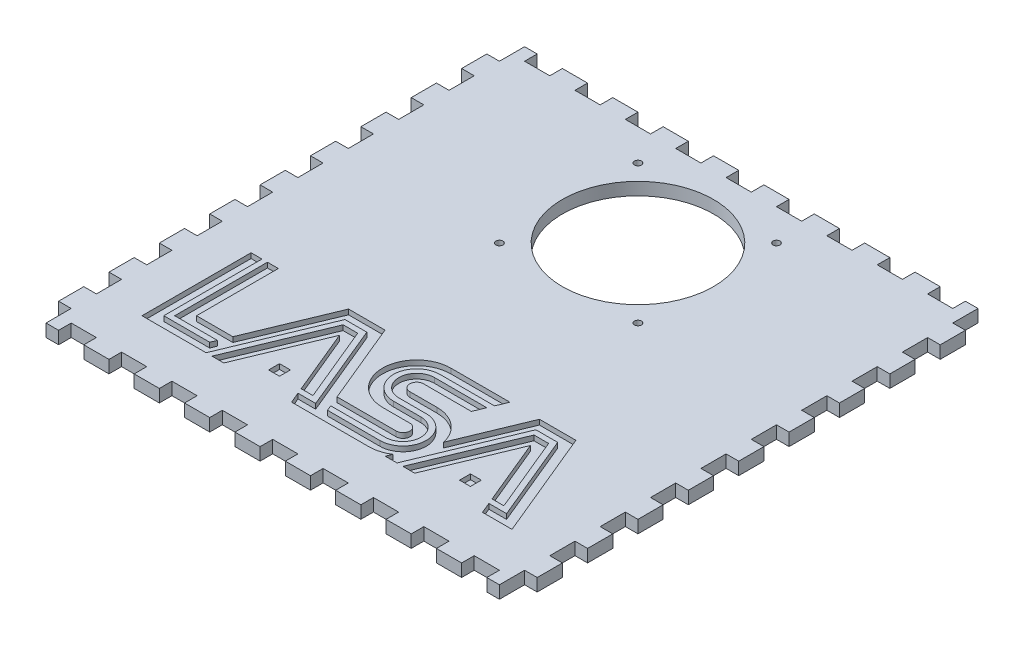
SolidWorks part; units mm, degrees
material "Pine"
ref_plane "Front Plane" through (0, 0, 0) normal (0, 0, 1) x (1, 0, 0)
ref_plane "Top Plane" through (0, 0, 0) normal (0, 1, 0) x (1, 0, 0)
ref_plane "Right Plane" through (0, 0, 0) normal (1, 0, 0) x (0, 0, -1)
sketch "Sketch1" plane through (0, 0, 0) normal (0, 1, 0) x (1, 0, 0)
  line L1 (0, 0) -> (241.3, 0)
  line L2 (0, 0) -> (0, 241.3)
  line L3 (0, 241.3) -> (241.3, 241.3)
  line L4 (241.3, 0) -> (241.3, 241.3)
  dimension "D1" = 241.3
  dimension "D2" = 241.3
extrude "Boss-Extrude1" add sketch "Sketch1" along normal blind 6.35
sketch "Sketch2" plane through (0, 6.35, 0) normal (0, 1, 0) x (1, 0, 0)
  line L1 (0, 241.3) -> (6.35, 241.3)
  line L2 (0, 241.3) -> (0, 228.6)
  line L3 (0, 228.6) -> (6.35, 228.6)
  line L4 (6.35, 241.3) -> (6.35, 228.6)
  line L5 (241.3, 241.3) -> (234.95, 241.3)
  line L6 (241.3, 241.3) -> (241.3, 228.6)
  line L7 (241.3, 228.6) -> (234.95, 228.6)
  line L8 (234.95, 241.3) -> (234.95, 228.6)
  dimension "D1" = 12.7
  dimension "D2" = 6.35
extrude "Cut-Extrude1" cut sketch "Sketch2" against normal through all
pattern_linear "LPattern1" count 10 spacing 25.4 along (0, 0, 1) of "Cut-Extrude1"
sketch "Sketch3" plane through (0, 6.35, 0) normal (0, 1, 0) x (1, 0, 0)
  line L0 (6.35, 0) -> (234.95, 0) construction
  line L1 (12.7, 0) -> (25.4, 0)
  line L2 (12.7, 0) -> (12.7, 6.35)
  line L3 (12.7, 6.35) -> (25.4, 6.35)
  line L4 (25.4, 0) -> (25.4, 6.35)
  line L5 (234.95, 241.3) -> (6.35, 241.3) construction
  line L6 (12.7, 241.3) -> (25.4, 241.3)
  line L7 (12.7, 241.3) -> (12.7, 234.95)
  line L8 (12.7, 234.95) -> (25.4, 234.95)
  line L9 (25.4, 241.3) -> (25.4, 234.95)
  line L10 (6.35, 0) -> (6.35, 12.7) construction
  point P12 (6.35, 6.35)
  dimension "D1" = 6.35
  dimension "D2" = 12.7
  dimension "D3" = 6.35
extrude "Cut-Extrude2" cut sketch "Sketch3" against normal through all
pattern_linear "LPattern2" count 9 spacing 25.4 along (1, 0, 0) of "Cut-Extrude2"
sketch "Sketch4" plane through (0, 6.35, 0) normal (0, 1, 0) x (1, 0, 0)
  line L1 (0, 203.2) -> (0, 190.5) construction
  line L3 (127, 0) -> (139.7, 0) construction
  circle A0 centre (120.65, 184.15) radius 38.1
  dimension "D3" = 76.2
  dimension "D1" = 120.65
  dimension "D2" = 184.15
extrude "Cut-Extrude3" cut sketch "Sketch4" against normal through all
sketch "Sketch8" plane through (0, 6.35, 0) normal (0, 1, 0) x (1, 0, 0)
  line L0 (35.6223, 82.3723) -> (41.1223, 82.3723)
  line L1 (157.8883, 82.3723) -> (155.6101, 76.8723)
  line L2 (155.6101, 76.8723) -> (128.0604, 76.8723)
  line L3 (128.0604, 53.4973) -> (141.8104, 53.4973)
  line L4 (141.8104, 35.6223) -> (114.2606, 35.6223)
  line L5 (114.2606, 35.6223) -> (115.3996, 32.8723)
  line L6 (115.3996, 32.8723) -> (141.8104, 32.8723)
  line L7 (141.8104, 56.2473) -> (128.0604, 56.2473)
  line L8 (128.0604, 74.1223) -> (154.471, 74.1223)
  line L9 (154.471, 74.1223) -> (152.1928, 68.6223)
  line L10 (196.7668, 32.8723) -> (199.0449, 27.3723)
  line L11 (196.7668, 32.8723) -> (205.6965, 32.8723)
  line L12 (205.6965, 32.8723) -> (187.4711, 76.8723)
  line L13 (187.4711, 76.8723) -> (176.4461, 76.8723)
  line L14 (176.4461, 76.8723) -> (155.9426, 27.3723)
  line L15 (149.9894, 27.3723) -> (155.9426, 27.3723)
  line L16 (100.5168, 32.8723) -> (102.7949, 27.3723)
  line L17 (100.5168, 32.8723) -> (109.4465, 32.8723)
  line L18 (109.4465, 32.8723) -> (91.2211, 76.8723)
  line L19 (91.2211, 76.8723) -> (80.1961, 76.8723)
  line L20 (80.1961, 76.8723) -> (59.6926, 27.3723)
  line L21 (27.3723, 27.3723) -> (59.6926, 27.3723)
  line L22 (27.3723, 82.3723) -> (32.8723, 82.3723)
  line L23 (32.8723, 82.3723) -> (32.8723, 32.8723)
  line L24 (32.8723, 32.8723) -> (56.0176, 32.8723)
  line L25 (56.0176, 32.8723) -> (57.1567, 35.6223)
  line L26 (57.1567, 35.6223) -> (35.6223, 35.6223)
  line L27 (35.6223, 35.6223) -> (35.6223, 82.3723)
  line L28 (41.1223, 82.3723) -> (41.1223, 41.1223)
  line L29 (41.1223, 41.1223) -> (59.4349, 41.1223)
  line L30 (59.4349, 41.1223) -> (76.5212, 82.3723)
  line L31 (76.5212, 82.3723) -> (94.8961, 82.3723)
  line L32 (94.8961, 82.3723) -> (111.9824, 41.1223)
  line L33 (111.9824, 41.1223) -> (141.8104, 41.1223)
  line L34 (141.8104, 47.9973) -> (128.0604, 47.9973)
  line L35 (128.0604, 82.3723) -> (157.8883, 82.3723)
  line L36 (128.0604, 68.6223) -> (152.1928, 68.6223)
  line L37 (141.8104, 61.7473) -> (128.0604, 61.7473)
  line L38 (158.6109, 48.1865) -> (172.7712, 82.3723)
  line L39 (172.7712, 82.3723) -> (191.1461, 82.3723)
  line L40 (213.9278, 27.3723) -> (191.1461, 82.3723)
  line L41 (199.0449, 27.3723) -> (213.9278, 27.3723)
  line L42 (151.1257, 30.1156) -> (149.9894, 27.3723)
  line L43 (102.7949, 27.3723) -> (141.8104, 27.3723)
  line L44 (27.3723, 27.3723) -> (27.3723, 82.3723)
  line L45 (88.4586, 35.6223) -> (82.9586, 35.6223)
  line L46 (82.9586, 35.6223) -> (82.9586, 41.1223)
  line L47 (88.4586, 41.1223) -> (82.9586, 41.1223)
  line L48 (88.4586, 35.6223) -> (88.4586, 41.1223)
  line L49 (179.2086, 41.1223) -> (184.7086, 41.1223)
  line L50 (184.7086, 35.6223) -> (184.7086, 41.1223)
  line L51 (179.2086, 35.6223) -> (184.7086, 35.6223)
  line L52 (179.2086, 35.6223) -> (179.2086, 41.1223)
  line L53 (178.2836, 74.1223) -> (185.6336, 74.1223)
  line L54 (185.6336, 74.1223) -> (201.5808, 35.6223)
  line L55 (201.5808, 35.6223) -> (195.6277, 35.6223)
  line L56 (181.9586, 68.6223) -> (195.6277, 35.6223)
  line L57 (158.9192, 27.3723) -> (164.8723, 27.3723)
  line L58 (164.8723, 27.3723) -> (181.9586, 68.6223)
  line L59 (158.9192, 27.3723) -> (178.2836, 74.1223)
  line L60 (85.7086, 68.6223) -> (99.3777, 35.6223)
  line L61 (68.6223, 27.3723) -> (85.7086, 68.6223)
  line L62 (62.6692, 27.3723) -> (68.6223, 27.3723)
  line L63 (82.0336, 74.1223) -> (89.3836, 74.1223)
  line L64 (89.3836, 74.1223) -> (105.3308, 35.6223)
  line L65 (105.3308, 35.6223) -> (99.3777, 35.6223)
  line L66 (62.6692, 27.3723) -> (82.0336, 74.1223)
  arc A0 (128.0604, 76.8723) -> (128.0604, 53.4973) centre (128.0604, 65.1848) ccw
  arc A1 (141.8104, 35.6223) -> (141.8104, 53.4973) centre (141.8104, 44.5598) ccw
  arc A2 (141.8104, 32.8723) -> (141.8104, 56.2473) centre (141.8104, 44.5598) ccw
  arc A3 (128.0604, 74.1223) -> (128.0604, 56.2473) centre (128.0604, 65.1848) ccw
  arc A4 (141.8104, 41.1223) -> (141.8104, 47.9973) centre (141.8104, 44.5598) ccw
  arc A5 (128.0604, 82.3723) -> (128.0604, 47.9973) centre (128.0604, 65.1848) ccw
  arc A6 (128.0604, 68.6223) -> (128.0604, 61.7473) centre (128.0604, 65.1848) ccw
  arc A7 (158.6109, 48.1865) -> (141.8104, 61.7473) centre (141.8104, 44.5598) ccw
  arc A8 (141.8104, 27.3723) -> (151.1257, 30.1156) centre (141.8104, 44.5598) ccw
extrude "Cut-Extrude4" cut sketch "Sketch8" against normal blind 2.54
sketch "Sketch9" plane through (0, 6.35, 0) normal (0, 1, 0) x (1, 0, 0)
  line L1 (155.575, 149.225) -> (85.725, 149.225) construction
  line L2 (155.575, 149.225) -> (155.575, 219.075) construction
  line L3 (155.575, 219.075) -> (85.725, 219.075) construction
  line L4 (85.725, 149.225) -> (85.725, 219.075) construction
  line L5 (155.575, 149.225) -> (85.725, 219.075) construction
  line L6 (155.575, 219.075) -> (85.725, 149.225) construction
  circle A0 centre (85.725, 219.075) radius 1.75
  point P0 (120.65, 184.15)
  dimension "D2" = 3.5
  dimension "D1" = 69.85
extrude "Cut-Extrude5" cut sketch "Sketch9" against normal through all
pattern_circular "CirPattern1" count 4 over 360 about axis through (120.65, 0, -184.15) along (0, 1, 0) of "Cut-Extrude5"
